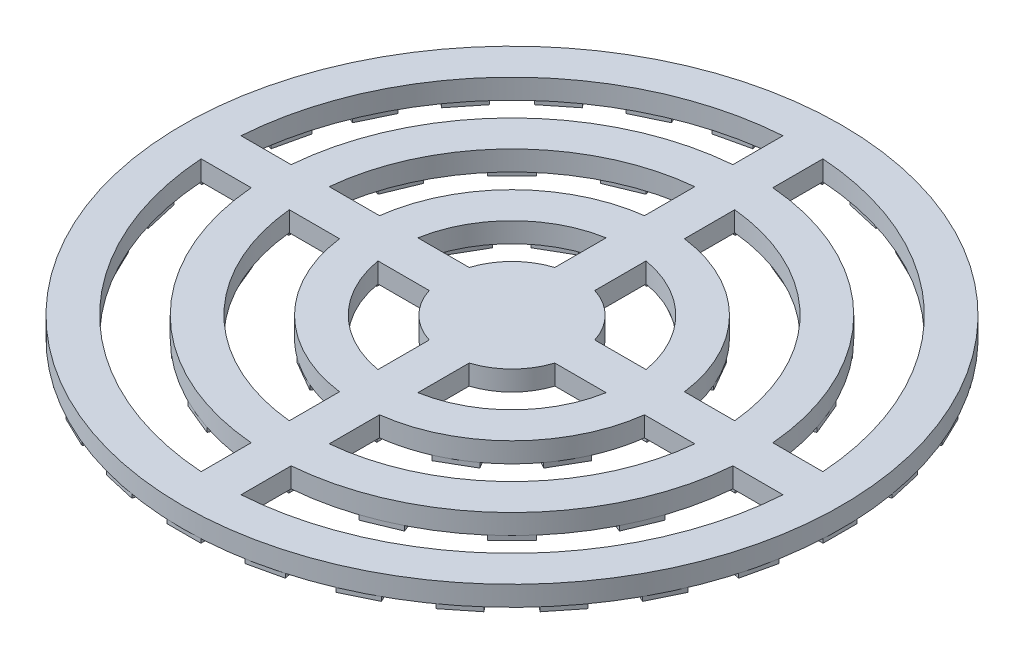
SolidWorks part; units mm, degrees
material "Plain Carbon Steel"
ref_plane "Front Plane" through (0, 0, 0) normal (0, 0, 1) x (1, 0, 0)
ref_plane "Top Plane" through (0, 0, 0) normal (0, 1, 0) x (1, 0, 0)
ref_plane "Right Plane" through (0, 0, 0) normal (1, 0, 0) x (0, 0, -1)
sketch "Sketch1" plane through (0, 0, 0) normal (0, 1, 0) x (1, 0, 0)
  circle A0 centre (0, 0) radius 33
  dimension "D1" = 66
extrude "Boss-Extrude1" add sketch "Sketch1" along normal blind 2
sketch "Sketch2" plane through (0, 2, 0) normal (0, 1, 0) x (1, 0, 0)
  line L0 (-33, 0) -> (33, 0) construction
  line L1 (-33, -2) -> (33, -2)
  line L2 (0, 33) -> (0, -33) construction
  line L3 (-2, 33) -> (-2, -33)
  line L4 (-33, 2) -> (33, 2)
  line L5 (2, 33) -> (2, -33)
  circle A0 centre (0, 0) radius 29.2
  circle A1 centre (0, 0) radius 24.2
  circle A2 centre (0, 0) radius 20.4
  circle A3 centre (0, 0) radius 15.4
  circle A4 centre (0, 0) radius 11.6
  circle A5 centre (0, 0) radius 33 construction
  circle A6 centre (0, 0) radius 6.6
  dimension "D3" = 3.8
  dimension "D4" = 3.8
  dimension "D5" = 3.8
  dimension "D6" = 5
  dimension "D7" = 5
  dimension "D8" = 5
  dimension "D1" = 2
  dimension "D2" = 2
extrude "Cut-Extrude1" cut sketch "Sketch2" against normal blind 2 contours A1 L1 A0 L3 | A1 L3 A0 L4 | A1 L4 A0 L5 | A1 L5 A0 L1 | A3 L5 A2 L1 | A3 L4 A2 L5 | A3 L3 A2 L4 | A3 L1 A2 L3 | A6 L1 A4 L3 | A6 L3 A4 L4 | A6 L4 A4 L5 | A6 L5 A4 L1
sketch "Sketch3" plane through (0, 0, 0) normal (0, -1, 0) x (-1, 0, 0)
  line L0 (0, 33) -> (0, 0) construction
  line L1 (-1.7, 29.35) -> (1.7, 29.35)
  line L2 (-1.7, 29.35) -> (-1.7, 32.85)
  line L3 (-1.7, 32.85) -> (1.7, 32.85)
  line L4 (1.7, 29.35) -> (1.7, 32.85)
  line L5 (-1.7, 29.35) -> (1.7, 32.85) construction
  line L6 (-1.7, 32.85) -> (1.7, 29.35) construction
  line L92 (-1.75, 24.1) -> (1.75, 24.1)
  line L93 (-1.75, 24.1) -> (-1.75, 20.6)
  line L94 (-1.75, 20.6) -> (1.75, 20.6)
  line L95 (1.75, 24.1) -> (1.75, 20.6)
  line L96 (-1.75, 24.1) -> (1.75, 20.6) construction
  line L97 (-1.75, 20.6) -> (1.75, 24.1) construction
  line L150 (-1.75, 11.75) -> (1.75, 11.75)
  line L151 (-1.75, 11.75) -> (-1.75, 15.25)
  line L152 (-1.75, 15.25) -> (1.75, 15.25)
  line L153 (1.75, 11.75) -> (1.75, 15.25)
  line L154 (-1.75, 11.75) -> (1.75, 15.25) construction
  line L155 (-1.75, 15.25) -> (1.75, 11.75) construction
  line L188 (4.8736, 28.9924) -> (8.1884, 28.2358)
  line L189 (8.1884, 28.2358) -> (8.9672, 31.6481)
  line L190 (5.6524, 32.4047) -> (8.9672, 31.6481)
  line L191 (4.8736, 28.9924) -> (5.6524, 32.4047)
  line L192 (11.2028, 27.181) -> (14.2661, 25.7058)
  line L193 (14.2661, 25.7058) -> (15.7847, 28.8592)
  line L194 (12.7214, 30.3344) -> (15.7847, 28.8592)
  line L195 (11.2028, 27.181) -> (12.7214, 30.3344)
  line L196 (16.9703, 24.0067) -> (19.6285, 21.8868)
  line L197 (19.6285, 21.8868) -> (21.8108, 24.6232)
  line L198 (19.1525, 26.7431) -> (21.8108, 24.6232)
  line L199 (16.9703, 24.0067) -> (19.1525, 26.7431)
  line L200 (21.8868, 19.6285) -> (24.0067, 16.9703)
  line L201 (24.0067, 16.9703) -> (26.7431, 19.1525)
  line L202 (24.6232, 21.8108) -> (26.7431, 19.1525)
  line L203 (21.8868, 19.6285) -> (24.6232, 21.8108)
  line L204 (25.7058, 14.2661) -> (27.181, 11.2028)
  line L205 (27.181, 11.2028) -> (30.3344, 12.7214)
  line L206 (28.8592, 15.7847) -> (30.3344, 12.7214)
  line L207 (25.7058, 14.2661) -> (28.8592, 15.7847)
  line L208 (28.2358, 8.1884) -> (28.9924, 4.8736)
  line L209 (28.9924, 4.8736) -> (32.4047, 5.6524)
  line L210 (31.6481, 8.9672) -> (32.4047, 5.6524)
  line L211 (28.2358, 8.1884) -> (31.6481, 8.9672)
  line L212 (29.35, 1.7) -> (29.35, -1.7)
  line L213 (29.35, -1.7) -> (32.85, -1.7)
  line L214 (32.85, 1.7) -> (32.85, -1.7)
  line L215 (29.35, 1.7) -> (32.85, 1.7)
  line L216 (28.9924, -4.8736) -> (28.2358, -8.1884)
  line L217 (28.2358, -8.1884) -> (31.6481, -8.9672)
  line L218 (32.4047, -5.6524) -> (31.6481, -8.9672)
  line L219 (28.9924, -4.8736) -> (32.4047, -5.6524)
  line L220 (27.181, -11.2028) -> (25.7058, -14.2661)
  line L221 (25.7058, -14.2661) -> (28.8592, -15.7847)
  line L222 (30.3344, -12.7214) -> (28.8592, -15.7847)
  line L223 (27.181, -11.2028) -> (30.3344, -12.7214)
  line L224 (24.0067, -16.9703) -> (21.8868, -19.6285)
  line L225 (21.8868, -19.6285) -> (24.6232, -21.8108)
  line L226 (26.7431, -19.1525) -> (24.6232, -21.8108)
  line L227 (24.0067, -16.9703) -> (26.7431, -19.1525)
  line L228 (19.6285, -21.8868) -> (16.9703, -24.0067)
  line L229 (16.9703, -24.0067) -> (19.1525, -26.7431)
  line L230 (21.8108, -24.6232) -> (19.1525, -26.7431)
  line L231 (19.6285, -21.8868) -> (21.8108, -24.6232)
  line L232 (14.2661, -25.7058) -> (11.2028, -27.181)
  line L233 (11.2028, -27.181) -> (12.7214, -30.3344)
  line L234 (15.7847, -28.8592) -> (12.7214, -30.3344)
  line L235 (14.2661, -25.7058) -> (15.7847, -28.8592)
  line L236 (8.1884, -28.2358) -> (4.8736, -28.9924)
  line L237 (4.8736, -28.9924) -> (5.6524, -32.4047)
  line L238 (8.9672, -31.6481) -> (5.6524, -32.4047)
  line L239 (8.1884, -28.2358) -> (8.9672, -31.6481)
  line L240 (1.7, -29.35) -> (-1.7, -29.35)
  line L241 (-1.7, -29.35) -> (-1.7, -32.85)
  line L242 (1.7, -32.85) -> (-1.7, -32.85)
  line L243 (1.7, -29.35) -> (1.7, -32.85)
  line L244 (-4.8736, -28.9924) -> (-8.1884, -28.2358)
  line L245 (-8.1884, -28.2358) -> (-8.9672, -31.6481)
  line L246 (-5.6524, -32.4047) -> (-8.9672, -31.6481)
  line L247 (-4.8736, -28.9924) -> (-5.6524, -32.4047)
  line L248 (-11.2028, -27.181) -> (-14.2661, -25.7058)
  line L249 (-14.2661, -25.7058) -> (-15.7847, -28.8592)
  line L250 (-12.7214, -30.3344) -> (-15.7847, -28.8592)
  line L251 (-11.2028, -27.181) -> (-12.7214, -30.3344)
  line L252 (-16.9703, -24.0067) -> (-19.6285, -21.8868)
  line L253 (-19.6285, -21.8868) -> (-21.8108, -24.6232)
  line L254 (-19.1525, -26.7431) -> (-21.8108, -24.6232)
  line L255 (-16.9703, -24.0067) -> (-19.1525, -26.7431)
  line L256 (-21.8868, -19.6285) -> (-24.0067, -16.9703)
  line L257 (-24.0067, -16.9703) -> (-26.7431, -19.1525)
  line L258 (-24.6232, -21.8108) -> (-26.7431, -19.1525)
  line L259 (-21.8868, -19.6285) -> (-24.6232, -21.8108)
  line L260 (-25.7058, -14.2661) -> (-27.181, -11.2028)
  line L261 (-27.181, -11.2028) -> (-30.3344, -12.7214)
  line L262 (-28.8592, -15.7847) -> (-30.3344, -12.7214)
  line L263 (-25.7058, -14.2661) -> (-28.8592, -15.7847)
  line L264 (-28.2358, -8.1884) -> (-28.9924, -4.8736)
  line L265 (-28.9924, -4.8736) -> (-32.4047, -5.6524)
  line L266 (-31.6481, -8.9672) -> (-32.4047, -5.6524)
  line L267 (-28.2358, -8.1884) -> (-31.6481, -8.9672)
  line L268 (-29.35, -1.7) -> (-29.35, 1.7)
  line L269 (-29.35, 1.7) -> (-32.85, 1.7)
  line L270 (-32.85, -1.7) -> (-32.85, 1.7)
  line L271 (-29.35, -1.7) -> (-32.85, -1.7)
  line L272 (-28.9924, 4.8736) -> (-28.2358, 8.1884)
  line L273 (-28.2358, 8.1884) -> (-31.6481, 8.9672)
  line L274 (-32.4047, 5.6524) -> (-31.6481, 8.9672)
  line L275 (-28.9924, 4.8736) -> (-32.4047, 5.6524)
  line L276 (-27.181, 11.2028) -> (-25.7058, 14.2661)
  line L277 (-25.7058, 14.2661) -> (-28.8592, 15.7847)
  line L278 (-30.3344, 12.7214) -> (-28.8592, 15.7847)
  line L279 (-27.181, 11.2028) -> (-30.3344, 12.7214)
  line L280 (-24.0067, 16.9703) -> (-21.8868, 19.6285)
  line L281 (-21.8868, 19.6285) -> (-24.6232, 21.8108)
  line L282 (-26.7431, 19.1525) -> (-24.6232, 21.8108)
  line L283 (-24.0067, 16.9703) -> (-26.7431, 19.1525)
  line L284 (-19.6285, 21.8868) -> (-16.9703, 24.0067)
  line L285 (-16.9703, 24.0067) -> (-19.1525, 26.7431)
  line L286 (-21.8108, 24.6232) -> (-19.1525, 26.7431)
  line L287 (-19.6285, 21.8868) -> (-21.8108, 24.6232)
  line L288 (-14.2661, 25.7058) -> (-11.2028, 27.181)
  line L289 (-11.2028, 27.181) -> (-12.7214, 30.3344)
  line L290 (-15.7847, 28.8592) -> (-12.7214, 30.3344)
  line L291 (-14.2661, 25.7058) -> (-15.7847, 28.8592)
  line L292 (-8.1884, 28.2358) -> (-4.8736, 28.9924)
  line L293 (-4.8736, 28.9924) -> (-5.6524, 32.4047)
  line L294 (-8.9672, 31.6481) -> (-5.6524, 32.4047)
  line L295 (-8.1884, 28.2358) -> (-8.9672, 31.6481)
  line L296 (7.6059, 22.9352) -> (10.8395, 21.5958)
  line L297 (10.8395, 21.5958) -> (9.5001, 18.3622)
  line L298 (6.2665, 19.7016) -> (9.5001, 18.3622)
  line L299 (7.6059, 22.9352) -> (6.2665, 19.7016)
  line L300 (15.8038, 18.2787) -> (18.2787, 15.8038)
  line L301 (18.2787, 15.8038) -> (15.8038, 13.329)
  line L302 (13.329, 15.8038) -> (15.8038, 13.329)
  line L303 (15.8038, 18.2787) -> (13.329, 15.8038)
  line L304 (21.5958, 10.8395) -> (22.9352, 7.6059)
  line L305 (22.9352, 7.6059) -> (19.7016, 6.2665)
  line L306 (18.3622, 9.5001) -> (19.7016, 6.2665)
  line L307 (21.5958, 10.8395) -> (18.3622, 9.5001)
  line L308 (24.1, 1.75) -> (24.1, -1.75)
  line L309 (24.1, -1.75) -> (20.6, -1.75)
  line L310 (20.6, 1.75) -> (20.6, -1.75)
  line L311 (24.1, 1.75) -> (20.6, 1.75)
  line L312 (22.9352, -7.6059) -> (21.5958, -10.8395)
  line L313 (21.5958, -10.8395) -> (18.3622, -9.5001)
  line L314 (19.7016, -6.2665) -> (18.3622, -9.5001)
  line L315 (22.9352, -7.6059) -> (19.7016, -6.2665)
  line L316 (18.2787, -15.8038) -> (15.8038, -18.2787)
  line L317 (15.8038, -18.2787) -> (13.329, -15.8038)
  line L318 (15.8038, -13.329) -> (13.329, -15.8038)
  line L319 (18.2787, -15.8038) -> (15.8038, -13.329)
  line L320 (10.8395, -21.5958) -> (7.6059, -22.9352)
  line L321 (7.6059, -22.9352) -> (6.2665, -19.7016)
  line L322 (9.5001, -18.3622) -> (6.2665, -19.7016)
  line L323 (10.8395, -21.5958) -> (9.5001, -18.3622)
  line L324 (1.75, -24.1) -> (-1.75, -24.1)
  line L325 (-1.75, -24.1) -> (-1.75, -20.6)
  line L326 (1.75, -20.6) -> (-1.75, -20.6)
  line L327 (1.75, -24.1) -> (1.75, -20.6)
  line L328 (-7.6059, -22.9352) -> (-10.8395, -21.5958)
  line L329 (-10.8395, -21.5958) -> (-9.5001, -18.3622)
  line L330 (-6.2665, -19.7016) -> (-9.5001, -18.3622)
  line L331 (-7.6059, -22.9352) -> (-6.2665, -19.7016)
  line L332 (-15.8038, -18.2787) -> (-18.2787, -15.8038)
  line L333 (-18.2787, -15.8038) -> (-15.8038, -13.329)
  line L334 (-13.329, -15.8038) -> (-15.8038, -13.329)
  line L335 (-15.8038, -18.2787) -> (-13.329, -15.8038)
  line L336 (-21.5958, -10.8395) -> (-22.9352, -7.6059)
  line L337 (-22.9352, -7.6059) -> (-19.7016, -6.2665)
  line L338 (-18.3622, -9.5001) -> (-19.7016, -6.2665)
  line L339 (-21.5958, -10.8395) -> (-18.3622, -9.5001)
  line L340 (-24.1, -1.75) -> (-24.1, 1.75)
  line L341 (-24.1, 1.75) -> (-20.6, 1.75)
  line L342 (-20.6, -1.75) -> (-20.6, 1.75)
  line L343 (-24.1, -1.75) -> (-20.6, -1.75)
  line L344 (-22.9352, 7.6059) -> (-21.5958, 10.8395)
  line L345 (-21.5958, 10.8395) -> (-18.3622, 9.5001)
  line L346 (-19.7016, 6.2665) -> (-18.3622, 9.5001)
  line L347 (-22.9352, 7.6059) -> (-19.7016, 6.2665)
  line L348 (-18.2787, 15.8038) -> (-15.8038, 18.2787)
  line L349 (-15.8038, 18.2787) -> (-13.329, 15.8038)
  line L350 (-15.8038, 13.329) -> (-13.329, 15.8038)
  line L351 (-18.2787, 15.8038) -> (-15.8038, 13.329)
  line L352 (-10.8395, 21.5958) -> (-7.6059, 22.9352)
  line L353 (-7.6059, 22.9352) -> (-6.2665, 19.7016)
  line L354 (-9.5001, 18.3622) -> (-6.2665, 19.7016)
  line L355 (-10.8395, 21.5958) -> (-9.5001, 18.3622)
  line L356 (7.4001, 9.2982) -> (9.1501, 12.3293)
  line L357 (6.119, 14.0793) -> (9.1501, 12.3293)
  line L358 (4.369, 11.0482) -> (6.119, 14.0793)
  line L359 (4.369, 11.0482) -> (7.4001, 9.2982)
  line L360 (11.0673, 4.3499) -> (14.0984, 6.0999)
  line L361 (12.3484, 9.131) -> (14.0984, 6.0999)
  line L362 (9.3173, 7.381) -> (12.3484, 9.131)
  line L363 (9.3173, 7.381) -> (11.0673, 4.3499)
  line L364 (11.7691, -1.7691) -> (15.2691, -1.7691)
  line L365 (15.2691, 1.7309) -> (15.2691, -1.7691)
  line L366 (11.7691, 1.7309) -> (15.2691, 1.7309)
  line L367 (11.7691, 1.7309) -> (11.7691, -1.7691)
  line L368 (9.3173, -7.4191) -> (12.3484, -9.1691)
  line L369 (14.0984, -6.138) -> (12.3484, -9.1691)
  line L370 (11.0673, -4.388) -> (14.0984, -6.138)
  line L371 (11.0673, -4.388) -> (9.3173, -7.4191)
  line L372 (4.369, -11.0864) -> (6.119, -14.1174)
  line L373 (9.1501, -12.3674) -> (6.119, -14.1174)
  line L374 (7.4001, -9.3364) -> (9.1501, -12.3674)
  line L375 (7.4001, -9.3364) -> (4.369, -11.0864)
  line L376 (-1.75, -11.7881) -> (-1.75, -15.2881)
  line L377 (1.75, -15.2881) -> (-1.75, -15.2881)
  line L378 (1.75, -11.7881) -> (1.75, -15.2881)
  line L379 (1.75, -11.7881) -> (-1.75, -11.7881)
  line L380 (-7.4001, -9.3364) -> (-9.1501, -12.3674)
  line L381 (-6.119, -14.1174) -> (-9.1501, -12.3674)
  line L382 (-4.369, -11.0864) -> (-6.119, -14.1174)
  line L383 (-4.369, -11.0864) -> (-7.4001, -9.3364)
  line L384 (-11.0673, -4.388) -> (-14.0984, -6.138)
  line L385 (-12.3484, -9.1691) -> (-14.0984, -6.138)
  line L386 (-9.3173, -7.4191) -> (-12.3484, -9.1691)
  line L387 (-9.3173, -7.4191) -> (-11.0673, -4.388)
  line L388 (-11.7691, 1.7309) -> (-15.2691, 1.7309)
  line L389 (-15.2691, -1.7691) -> (-15.2691, 1.7309)
  line L390 (-11.7691, -1.7691) -> (-15.2691, -1.7691)
  line L391 (-11.7691, -1.7691) -> (-11.7691, 1.7309)
  line L392 (-9.3173, 7.381) -> (-12.3484, 9.131)
  line L393 (-14.0984, 6.0999) -> (-12.3484, 9.131)
  line L394 (-11.0673, 4.3499) -> (-14.0984, 6.0999)
  line L395 (-11.0673, 4.3499) -> (-9.3173, 7.381)
  line L396 (-4.369, 11.0482) -> (-6.119, 14.0793)
  line L397 (-9.1501, 12.3293) -> (-6.119, 14.0793)
  line L398 (-7.4001, 9.2982) -> (-9.1501, 12.3293)
  line L399 (-7.4001, 9.2982) -> (-4.369, 11.0482)
  line L400 (-5.1265, 2.6517) -> (-2.6517, 0.1768)
  line L409 (-2.6517, 0.1768) -> (-0.1768, 2.6517)
  line L410 (-0.1768, 2.6517) -> (-2.6517, 5.1265)
  line L411 (-2.6517, 5.1265) -> (-5.1265, 2.6517)
  line L412 (0, 0) -> (-4.6669, 4.6669) construction
  line L413 (5.1265, 2.6517) -> (2.6517, 5.1265)
  line L414 (2.6517, 5.1265) -> (0.1768, 2.6517)
  line L415 (0.1768, 2.6517) -> (2.6517, 0.1768)
  line L416 (2.6517, 0.1768) -> (5.1265, 2.6517)
  line L417 (2.6517, -5.1265) -> (5.1265, -2.6517)
  line L418 (5.1265, -2.6517) -> (2.6517, -0.1768)
  line L419 (2.6517, -0.1768) -> (0.1768, -2.6517)
  line L420 (0.1768, -2.6517) -> (2.6517, -5.1265)
  line L421 (-5.1265, -2.6517) -> (-2.6517, -5.1265)
  line L422 (-2.6517, -5.1265) -> (-0.1768, -2.6517)
  line L423 (-0.1768, -2.6517) -> (-2.6517, -0.1768)
  line L424 (-2.6517, -0.1768) -> (-5.1265, -2.6517)
  line L425 (-2.6517, 5.1265) -> (-2.6517, 0.1768) construction
  circle A0 centre (0, 0) radius 33 construction
  arc A1 (-2, 6.2897) -> (-6.2897, 2) centre (0, 0) ccw construction
  point P0 (0, 31.1)
  point P10 (0, 22.35)
  point P99 (0, 13.5)
  point P236 (-3.8891, 3.8891)
  point P237 (-1.4142, 1.4142)
  point P238 (-2.6517, 2.6517)
  point P239 (0, 0)
  dimension "D1" = 3.5
  dimension "D2" = 3.4
  dimension "D3" = 1.9
  dimension "D5" = 3.5
  dimension "D6" = 3.5
  dimension "D9" = 3.5
  dimension "D10" = 3.5
  dimension "D11" = 19.5
  dimension "D4" = 10.65
  dimension "D7" = 3.5
  dimension "D8" = 2
  dimension "D13" = 28
  dimension "D12" = 16
  dimension "D14" = 12
extrude "Boss-Extrude2" add sketch "Sketch3" along normal blind 0.5
equation "\"D4@Sketch2\"=\"D3@Sketch2\""
equation "\"D5@Sketch2\"=\"D3@Sketch2\""
equation "\"D6@Sketch2\"=\"D7@Sketch2\""
equation "\"D8@Sketch2\"=\"D7@Sketch2\""
equation "\"D11@Sketch3\"=5+5+7+0.6+3.8/2mm"
